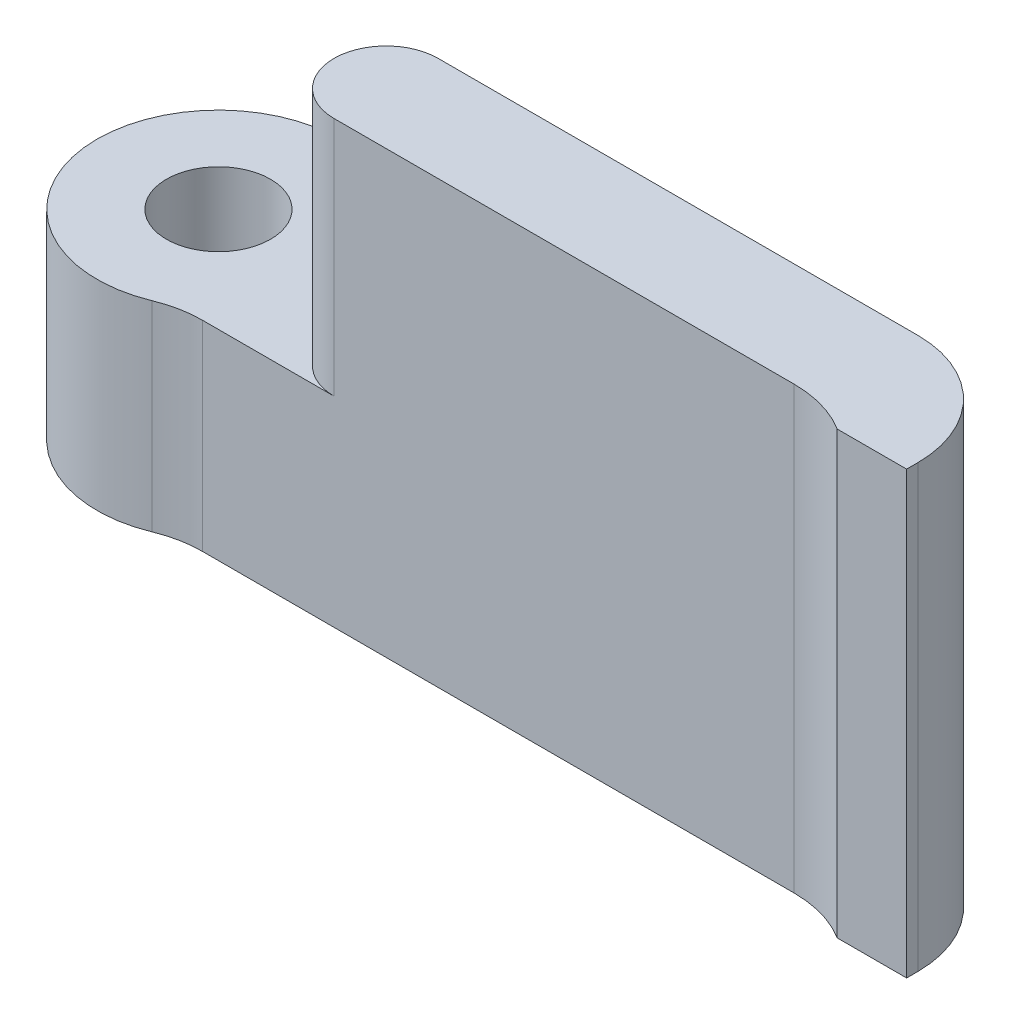
SolidWorks part; units mm, degrees
ref_plane "Front Plane" through (0, 0, 0) normal (0, 0, 1) x (1, 0, 0)
ref_plane "Top Plane" through (0, 0, 0) normal (0, 1, 0) x (1, 0, 0)
ref_plane "Right Plane" through (0, 0, 0) normal (1, 0, 0) x (0, 0, -1)
sketch "Sketch1" plane through (0, 0, 0) normal (0, 1, 0) x (1, 0, 0)
  line L0 (3.5, 0) -> (23.3302, 0)
  line L1 (23.3302, 0) -> (23.3302, 3)
  line L2 (23.3302, 3) -> (1.8028, 3)
  line L3 (23.3302, 4) -> (23.3302, 7) construction
  line L4 (0, 4) -> (23.3302, 4) construction
  circle A0 centre (0, 0) radius 3.5
  dimension "D1" = 7
  dimension "D2" = 3
  dimension "D3" = 1
extrude "Boss-Extrude1" add sketch "Sketch1" along normal blind 12.7
sketch "Sketch2" plane through (0, 12.7, 0) normal (0, 1, 0) x (1, 0, 0)
  line L0 (3.5, 0) -> (23.3302, 0) construction
  line L1 (23.3302, 3) -> (1.8028, 3) construction
  line L2 (6.3302, 0) -> (6.3302, 3) construction
  line L3 (23.3302, 0) -> (23.3302, 3) construction
  arc A0 (6.3302, 0) -> (6.3302, 3) centre (6.3302, 1.5) cw
  arc A1 (6.3302, 0) -> (6.3302, 3) centre (0.1803, 1.5) cw
  line M3 (23.3302, 3) -> (1.8028, 3)
  arc M4 (1.8028, 3) -> (3.5, 0) centre (0, 0) ccw
  line M5 (3.5, 0) -> (23.3302, 0)
  dimension "D1" = 17
extrude "Cut-Extrude1" cut sketch "Sketch2" against normal up to surface (6.93 mm away) contours A1 M5 M4 M3 | A0 M5 M3 M4
sketch "Sketch3" plane through (0, 5.77, 0) normal (0, 1, 0) x (1, 0, 0)
  circle A0 centre (0, 0) radius 1.5
  dimension "D1" = 3
extrude "Cut-Extrude2" cut sketch "Sketch3" against normal through all
ref_plane "Plane1" through (0, 0, -5) normal (0, 0, 1) x (1, 0, 0)
mirror "Mirror1" about plane through (0, 0, -5) normal (0, 0, 1) of bodies 103
delete or keep bodies "Body-Delete1" type delete bodies bodies 103
sketch "Sketch4" plane through (0, 0, -7) normal (0, 0, 1) x (1, 0, 0)
  circle A0 centre (59.2853, -42.8314) radius 2
  circle A1 centre (59.2853, -47.5314) radius 2
  dimension "D1" = 4
extrude "Cut-Extrude3" cut sketch "Sketch4" against normal blind 10
sketch "Sketch5" plane through (0, 12.7, 0) normal (0, 1, 0) x (1, 0, 0)
  line L0 (23.3302, 7) -> (6.3302, 7) construction
  line L1 (23.3302, 7) -> (21.3302, 7)
  line L2 (23.3302, 7) -> (23.3302, 6.5)
  line L3 (23.3302, 6.5) -> (21.3302, 6.5)
  line L4 (21.3302, 7) -> (21.3302, 6.5)
  arc A0 (21.3302, 6.5) -> (19.591, 7) centre (19.591, 3.725) ccw
  arc A1 (19.591, 2) -> (21.3302, 2.5) centre (19.591, 5.275) ccw construction
  line M2 (6.3302, 7) -> (23.3302, 7)
  dimension "D1" = 0.5
  dimension "D2" = 2
extrude "Boss-Extrude2" add sketch "Sketch5" against normal up to surface (12.7 mm away) contours A0 L4 M2 | L4 L3 L2 M2
fillet "Fillet1" radius 3.175 3 edges at (23.3302, 6.35, -10) (3.5, 2.885, -10) (1.8028, 2.885, -7)
sketch "Sketch6" plane through (0, 0, -7) normal (0, 0, 1) x (1, 0, 0)
  circle A0 centre (66.7439, -45.1814) radius 1.585
  circle A1 centre (66.7439, -45.1814) radius 1.585 construction
extrude "Cut-Extrude4" cut sketch "Sketch6" against normal blind 1.5
